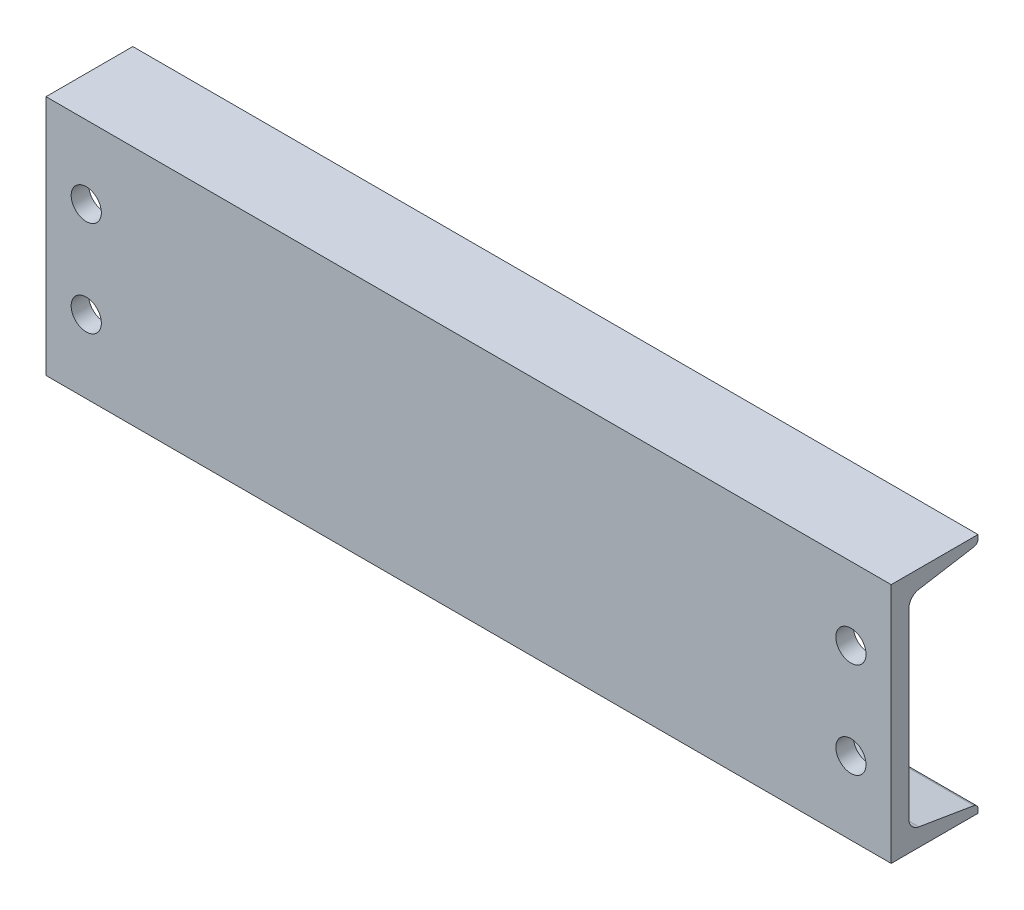
SolidWorks part; units mm, degrees
ref_plane "Front Plane" through (0, 0, 0) normal (0, 0, 1) x (1, 0, 0)
ref_plane "Top Plane" through (0, 0, 0) normal (0, 1, 0) x (1, 0, 0)
ref_plane "Right Plane" through (0, 0, 0) normal (1, 0, 0) x (0, 0, -1)
sketch "Sketch1" plane through (0, 0, 0) normal (1, 0, 0) x (0, 0, -1)
  line L0 (-27.3939, -76.2) -> (-27.3939, 76.2)
  line L1 (-27.3939, 76.2) -> (27.3939, 76.2)
  line L2 (-27.3939, -76.2) -> (27.3939, -76.2)
  line L3 (4.3561, -67.4878) -> (-21.0439, -67.4878) construction
  line L4 (-16.2941, 57.3918) -> (-16.2941, -57.3918)
  line L5 (27.3939, 76.2) -> (27.3939, 73.7107)
  line L6 (27.3939, -76.2) -> (27.3939, -73.7107)
  line L7 (-9.9269, 64.9081) -> (24.847, 70.7042)
  line L8 (-9.9269, -64.9081) -> (24.847, -70.7042)
  arc A0 (-16.2941, -57.3918) -> (-9.9269, -64.9081) centre (-8.6741, -57.3918) ccw
  arc A1 (-16.2941, 57.3918) -> (-9.9269, 64.9081) centre (-8.6741, 57.3918) cw
  arc A2 (27.3939, 73.7107) -> (24.847, 70.7042) centre (24.3459, 73.7107) cw
  arc A3 (27.3939, -73.7107) -> (24.847, -70.7042) centre (24.3459, -73.7107) ccw
extrude "Boss-Extrude1" add sketch "Sketch1" along normal mid plane 533.4
sketch "Sketch2" plane through (0, 0, 27.3939) normal (0, 0, 1) x (1, 0, 0)
  line L0 (0, 76.2) -> (0, -76.2) construction
  line L1 (266.7, 76.2) -> (-266.7, 76.2) construction
  line L2 (266.7, -76.2) -> (-266.7, -76.2) construction
  line L3 (-266.7, 0) -> (266.7, 0) construction
  line L4 (-266.7, 76.2) -> (-266.7, -76.2) construction
  line L5 (266.7, 76.2) -> (266.7, -76.2) construction
  circle A0 centre (-241.3, 30.1625) radius 9.525
  circle A1 centre (-241.3, -30.1625) radius 9.525
  circle A2 centre (241.3, -30.1625) radius 9.525
  circle A3 centre (241.3, 30.1625) radius 9.525
  dimension "D1" = 19.05
  dimension "D2" = 46.0375
  dimension "D3" = 25.4
extrude "Cut-Extrude1" cut sketch "Sketch2" against normal up to next
